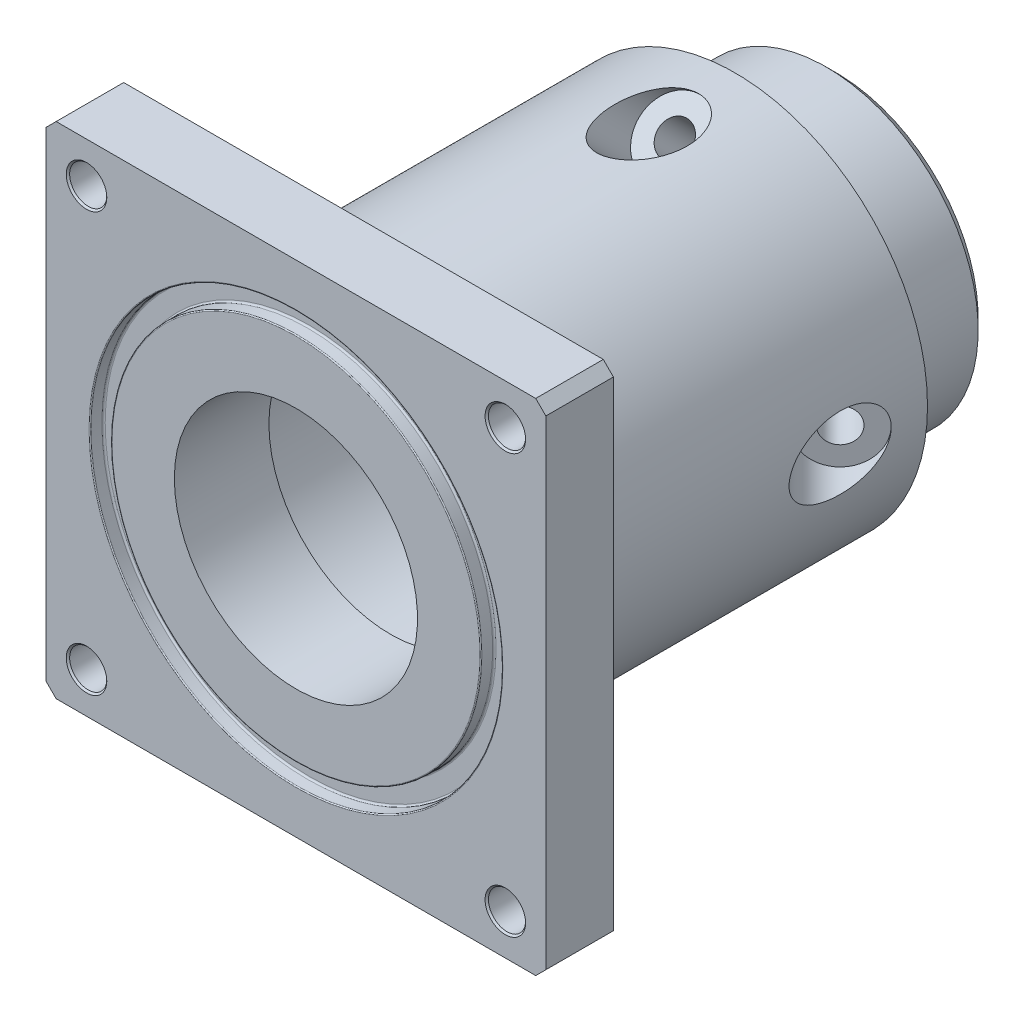
SolidWorks part; units mm, degrees
material "Bronze comercial , UNS C22000 (Bronze 90-10)"
ref_plane "Plano frontal" through (0, 0, 0) normal (0, 0, 1) x (1, 0, 0)
ref_plane "Plano superior" through (0, 0, 0) normal (0, 1, 0) x (1, 0, 0)
ref_plane "Plano direito" through (0, 0, 0) normal (1, 0, 0) x (0, 0, -1)
sketch "Esboço2" plane through (0, 0, 0) normal (1, 0, 0) x (0, 0, -1)
  line L0 (0, 20) -> (0, 52.5)
  line L1 (0, 52.5) -> (10, 52.5)
  line L2 (10, 52.5) -> (10, 28.5)
  line L3 (10, 28.5) -> (65, 28.5)
  line L4 (80, 22.5) -> (80, 20)
  line L5 (80, 0) -> (0, 0) construction
  line L6 (0, 0) -> (80, 0) construction
  line L7 (80, 20) -> (14, 20)
  line L8 (65, 28.5) -> (65, 22.5)
  line L9 (68, 22.5) -> (80, 22.5)
  line L10 (68, 22.5) -> (68, 21)
  line L11 (68, 21) -> (65, 21)
  line L12 (65, 21) -> (65, 22.5)
  line L13 (0, 20) -> (0, 18)
  line L14 (0, 18) -> (14, 18)
  line L15 (14, 18) -> (14, 20)
  dimension "D1" = 105
  dimension "D2" = 10
  dimension "D3" = 57
  dimension "D4" = 80
  dimension "D5" = 40
  dimension "D6" = 15
  dimension "D7" = 45
  dimension "D8" = 3
  dimension "D9" = 42
  dimension "D10" = 14
  dimension "D11" = 36
revolve "Revolução1" add sketch "Esboço2" angle 360 about L5
cosmetic thread "Representação de rosca1" parameters "D2"=42.516
cosmetic thread "Representação de rosca2" parameters "D1"=5, "D2"=39
hole_wizard "Furo com folga de M51" positions "Esboço7" profile "Esboço6" hole size "M5" standard "ISO" end condition through all
sketch "Esboço7" plane through (0, 0, 0) normal (0, 0, 1) x (1, 0, 0)
  line L4 (31, 31) -> (-31, 31) construction
  line L6 (31, 31) -> (31, -31) construction
  point P27 (-31, 31)
  point P29 (31, 31)
  point P31 (31, -31)
  point P33 (-31, -31)
  point P45 (0, 31)
  dimension "D1" = 62
  dimension "D2" = 62
sketch "Esboço6" plane through (-31, -31, 0) normal (1, 0, 0) x (0, -1, 0)
  line L0 (0, 0) -> (0, 80)
  line L1 (0, 80) -> (2.75, 80)
  line L2 (2.75, 80) -> (2.75, 0.25)
  line L3 (2.75, 0.25) -> (3, 0)
  line L5 (3, 0) -> (0, 0)
  line L6 (-2.75, 0.25) -> (-3, 0) construction
  line L11 (0, -6.35) -> (0, 107.95) construction
  dimension "Thru Hole Dia." = 5.5
  dimension "Thru Hole Depth" = 80
  dimension "Near C'Sink Dia." = 6
  dimension "Near C'Sink Angle" = 90
sketch "Esboço8" plane through (0, 0, 0) normal (0, 0, 1) x (1, 0, 0)
  line L1 (-37, 37) -> (37, 37)
  line L2 (-37, 37) -> (-37, -37)
  line L3 (-37, -37) -> (37, -37)
  line L4 (37, 37) -> (37, -37)
  line L5 (-37, 37) -> (37, -37) construction
  line L6 (-37, -37) -> (37, 37) construction
  circle A0 centre (0, 0) radius 52.5
  point P0 (0, 0)
  dimension "D1" = 74
  dimension "D2" = 74
extrude "Corte-extrusão1" cut sketch "Esboço8" against normal through all contours A0 | L2 L3 L4 L1
ref_plane "Plano1" through (28.5, 0, 0) normal (1, 0, 0) x (0, 0, -1)
ref_plane "Plano2" through (0, 0, -40) normal (0, 0, -1) x (-1, 0, 0)
ref_plane "Plano3" through (-5.75, 0, -5.75) normal (-0.7071, 0, -0.7071) x (-0.7071, 0, 0.7071)
ref_plane "Plano4" through (38.4684, 0, -15.9341) normal (-0.9239, 0, 0.3827) x (0.3827, 0, 0.9239)
ref_plane "Plano5" through (28.5, 0, 0) normal (1, 0, 0) x (0, 0, -1)
ref_plane "Plano6" through (20.1525, -20.1525, 0) normal (0.7071, -0.7071, 0) x (0, 0, -1)
ref_plane "Plano8" through (0, 0, 0) normal (0, 1, 0) x (1, 0, 0)
sketch "Esboço33" plane through (0, 0, 0) normal (0, 1, 0) x (1, 0, 0)
  line L0 (-22.7128, 54.3218) -> (-20.6976, 52.3065)
  line L1 (-15.8024, 61.2322) -> (-22.7128, 54.3218)
  line L2 (-31.9973, 41.0068) -> (-31.9973, 48.5728)
  line L3 (-31.9973, 48.5728) -> (-17.5701, 63)
  line L4 (-25, 80) -> (25, 80)
  line L5 (28.5, 80) -> (-28.5, 80) construction
  line L6 (-28.5, 65) -> (-28.5, 10) construction
  line L7 (-20.6976, 52.3065) -> (-31.9973, 41.0068)
  line L8 (-15.8024, 61.2322) -> (-17.5701, 63)
  dimension "D1" = 2.5
  dimension "D2" = 17
  dimension "D3" = 45
  dimension "D4" = 5.35
  dimension "D5" = 10.9299
  dimension "D6" = 9.7729
revolve "Corte-Revolução1" cut sketch "Esboço33" angle 360 about L3
pattern_circular "PadrãoCircular1" count 4 every 90 about axis through (0, 0, 0) along (0, 0, 1) of "Corte-Revolução1"
chamfer "Chanfro1" distance 1.5 angle 45 1 edges at (-22.5, 0, -80)
sketch "Esboço35" plane through (0, 0, 0) normal (0, 1, 0) x (1, 0, 0)
  line L0 (0, 0) -> (0, 121.7748) construction
  line L1 (-37, 0) -> (37, 0) construction
  line L2 (30.485, 0) -> (27.385, 0)
  line L3 (30.485, 0) -> (30.485, 2)
  line L4 (30.485, 2) -> (27.385, 2)
  line L5 (27.385, 0) -> (27.385, 2)
  point P9 (28.935, 0)
  dimension "D1" = 57.87
  dimension "D2" = 3.1
  dimension "D3" = 2
revolve "Corte-Revolução2" cut sketch "Esboço35" angle 360 about L0
fillet "Filete1" radius 0.25 2 edges at (27.385, 0, -2) (30.485, 0, -2)
fillet "Filete2" radius 0.15 2 edges at (27.385, 0, 0) (30.485, 0, 0)
chamfer "Chanfro2" distance 1.5 angle 45 4 edges at (37, -37, -5) (37, 37, -5) (-37, 37, -5) (-37, -37, -5)
fillet "Filete3" radius 1 1 edges at (-28.5, 0, -10)
